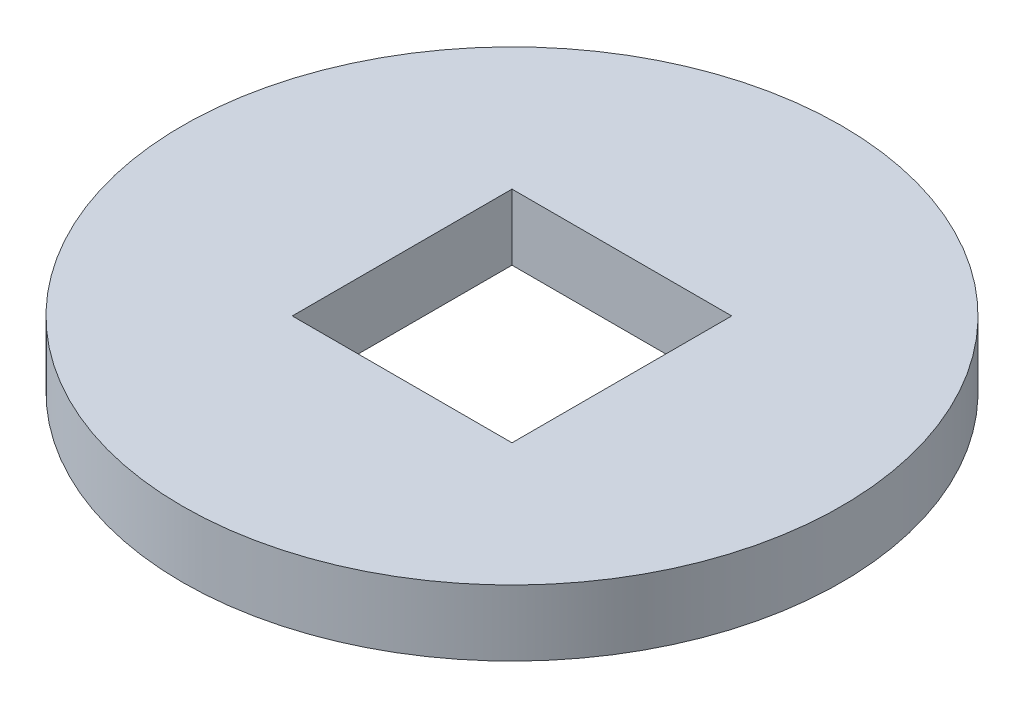
SolidWorks part; units mm, degrees
material "Stainless Steel (ferritic)"
ref_plane "Front Plane" through (0, 0, 0) normal (0, 0, 1) x (1, 0, 0)
ref_plane "Top Plane" through (0, 0, 0) normal (0, 1, 0) x (1, 0, 0)
ref_plane "Right Plane" through (0, 0, 0) normal (1, 0, 0) x (0, 0, -1)
sketch "Sketch1" plane through (0, 0, 0) normal (0, 1, 0) x (1, 0, 0)
  line L1 (-10, -10) -> (10, -10)
  line L2 (-10, -10) -> (-10, 10)
  line L3 (-10, 10) -> (10, 10)
  line L4 (10, -10) -> (10, 10)
  line L5 (-10, -10) -> (10, 10) construction
  line L6 (-10, 10) -> (10, -10) construction
  circle A0 centre (0, 0) radius 30
  dimension "D1" = 60
  dimension "D2" = 20
  dimension "D3" = 20
extrude "Boss-Extrude1" add sketch "Sketch1" along normal blind 6
